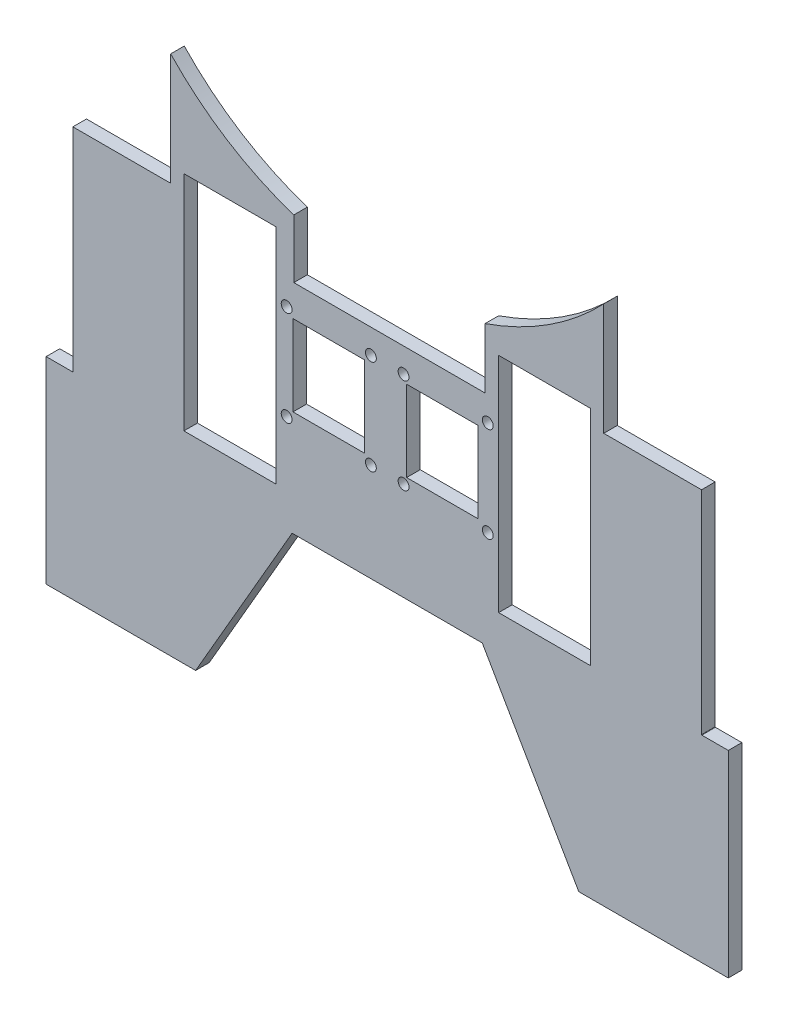
SolidWorks part; units mm, degrees
ref_plane "Front Plane" through (0, 0, 0) normal (0, 0, 1) x (1, 0, 0)
ref_plane "Top Plane" through (0, 0, 0) normal (0, 1, 0) x (1, 0, 0)
ref_plane "Right Plane" through (0, 0, 0) normal (1, 0, 0) x (0, 0, -1)
sketch "Sketch1" plane through (0, 0, 0) normal (0, 0, 1) x (1, 0, 0)
  line L157 (75.4494, -29.1887) -> (75.4494, 52.8429)
  line L158 (41.6114, -29.1887) -> (75.4494, -29.1887)
  line L159 (41.6114, 52.8429) -> (41.6114, -29.1887)
  line L160 (75.4494, 52.8429) -> (41.6114, 52.8429)
  line L161 (-74.2583, -29.1887) -> (-40.4202, -29.1887)
  line L162 (-40.4202, -29.1887) -> (-40.4202, 52.8429)
  line L163 (-74.2583, 52.8429) -> (-74.2583, -29.1887)
  line L164 (-40.4202, 52.8429) -> (-74.2583, 52.8429)
  line L165 (-67.3773, 102.2973) -> (-124.9367, 102.2973)
  line L166 (-124.9367, 102.2973) -> (-124.9535, 82.5555)
  line L169 (-124.9535, 82.5555) -> (-124.9586, 69.1219)
  line L170 (-124.9586, 69.1219) -> (-124.9589, 54.5006)
  line L171 (-124.9589, 54.5006) -> (-115.1164, 54.5006)
  line L172 (-115.1164, 54.5006) -> (-115.1164, -30.8464)
  line L173 (-115.1164, -30.8464) -> (-124.9602, -30.8464)
  line L174 (-124.9602, -30.8464) -> (-124.9602, -103.4029)
  line L175 (-124.9602, -103.4029) -> (-69.9272, -103.4029)
  line L176 (-69.9272, -103.4029) -> (-34.4065, -41.8792)
  line L177 (-34.4065, -41.8792) -> (35.5976, -41.8792)
  line L178 (35.5976, -41.8792) -> (71.1183, -103.4029)
  line L179 (71.1183, -103.4029) -> (126.1513, -103.4029)
  line L180 (126.1513, -103.4029) -> (126.1513, -30.8464)
  line L181 (126.1513, -30.8464) -> (116.4345, -30.8464)
  line L182 (116.3075, -30.7195) -> (116.3075, 54.3736)
  line L183 (116.4345, 54.5006) -> (126.15, 54.5006)
  line L184 (126.15, 54.5006) -> (126.1497, 69.1118)
  line L185 (126.1497, 69.1118) -> (126.1446, 82.5656)
  line L186 (126.1446, 82.5656) -> (126.1279, 102.2973)
  line L187 (126.1279, 102.2973) -> (68.5684, 102.2973)
  arc A29 (-67.3773, 102.2973) -> (68.5684, 102.2973) centre (0.5956, 164.3939) ccw
  arc A30 (116.3075, -30.7195) -> (116.4345, -30.8464) centre (116.4345, -30.7195) ccw
  arc A31 (116.4345, 54.5006) -> (116.3075, 54.3736) centre (116.4345, 54.3736) ccw
  circle A32 centre (-5.4202, -5.6729) radius 2
  circle A33 centre (-36.4202, -5.6729) radius 2
  circle A34 centre (-36.4202, 29.3271) radius 2
  circle A35 centre (-5.4202, 29.3271) radius 2
  circle A36 centre (6.6114, 29.3271) radius 2
  circle A37 centre (6.6114, -5.6729) radius 2
  circle A38 centre (37.6114, -5.6729) radius 2
  circle A39 centre (37.6114, 29.3271) radius 2
extrude "Boss-Extrude1" add sketch "Sketch1" along normal blind 5
sketch "Sketch6" plane through (0, 0, 5) normal (0, 0, 1) x (1, 0, 0)
  line L0 (-36.4202, 29.3271) -> (-5.4202, -5.6729) construction
  line L1 (0, 0) -> (0, 20.5502) construction
  line L2 (-34.0996, 26.707) -> (-7.7409, 26.707)
  line L3 (-34.0996, 26.707) -> (-34.0996, -3.0529)
  line L4 (-34.0996, -3.0529) -> (-7.7409, -3.0529)
  line L5 (-7.7409, 26.707) -> (-7.7409, -3.0529)
  line L6 (-34.0996, 26.707) -> (-7.7409, -3.0529) construction
  line L7 (-34.0996, -3.0529) -> (-7.7409, 26.707) construction
  line L8 (34.0996, -3.0529) -> (7.7409, 26.707) construction
  line L9 (34.0996, 26.707) -> (7.7409, -3.0529) construction
  line L10 (7.7409, 26.707) -> (7.7409, -3.0529)
  line L11 (34.0996, -3.0529) -> (7.7409, -3.0529)
  line L12 (34.0996, 26.707) -> (34.0996, -3.0529)
  line L13 (34.0996, 26.707) -> (7.7409, 26.707)
  point P4 (-20.9202, 11.8271)
  point P16 (20.9202, 11.8271)
  dimension "D1" = 3.5
extrude "Cut-Extrude5" cut sketch "Sketch6" against normal blind 10
sketch "Sketch7" plane through (0, 0, 5) normal (0, 0, 1) x (1, 0, 0)
  line L0 (30.5956, 58.3271) -> (-29.4044, 58.3271) construction
  line L1 (30.5956, 72.3271) -> (30.5956, 44.3271) construction
  line L2 (-29.4044, 44.3271) -> (-29.4044, 72.3271) construction
  line L3 (41.6114, 34.3271) -> (2.6114, 34.3271) construction
  line L5 (36.6114, 79.276) -> (36.6114, 38.3271)
  line L6 (36.6114, 38.3271) -> (-33.7889, 38.3271)
  line L7 (-33.7889, 77.4212) -> (-33.7889, 38.3271)
  line L8 (36.6114, 79.276) -> (-33.7889, 38.3271) construction
  line L9 (36.6114, 38.3271) -> (-33.7889, 77.4212) construction
  line L10 (41.6114, 52.8429) -> (41.6114, -29.1887) construction
  line L13 (36.6114, 79.276) -> (36.6114, 95.1212)
  line L14 (36.6114, 95.1212) -> (-33.7889, 95.1212)
  line L15 (-33.7889, 77.4212) -> (-33.7889, 95.1212)
  line L16 (36.6114, 79.276) -> (-33.7889, 95.1212) construction
  line L17 (36.6114, 95.1212) -> (-33.7889, 77.4212) construction
  point P7 (0.5956, 58.3271)
  point P19 (3.3575, 86.7605)
  dimension "D1" = 4
  dimension "D2" = 5
extrude "Cut-Extrude7" cut sketch "Sketch7" against normal blind 10
sketch "Sketch8" plane through (0, 0, 0) normal (0, 0, -1) x (-1, 0, 0)
  circle A0 centre (-0.5956, 164.3939) radius 110
  dimension "D1" = 220
extrude "Cut-Extrude8" cut sketch "Sketch8" against normal blind 10
sketch "Sketch9" plane through (0, 0, 5) normal (0, 0, 1) x (1, 0, 0)
  line L1 (-124.9367, 110.3271) -> (-90.201, 110.3271)
  line L2 (-124.9367, 110.3271) -> (-124.9367, 102.2973)
  line L3 (-124.9367, 102.2973) -> (-90.201, 102.2973)
  line L4 (-90.201, 110.3271) -> (-90.201, 102.2973)
  line L5 (-124.9367, 110.3271) -> (-90.201, 102.2973) construction
  line L6 (-124.9367, 102.2973) -> (-90.201, 110.3271) construction
  line L7 (126.1279, 110.3271) -> (91.3922, 110.3271)
  line L8 (126.1279, 110.3271) -> (126.1279, 102.2973)
  line L9 (126.1279, 102.2973) -> (91.3922, 102.2973)
  line L10 (91.3922, 110.3271) -> (91.3922, 102.2973)
  line L11 (126.1279, 110.3271) -> (91.3922, 102.2973) construction
  line L12 (126.1279, 102.2973) -> (91.3922, 110.3271) construction
  point P4 (-107.5689, 106.3122)
  point P11 (108.76, 106.3122)
extrude "Boss-Extrude2" add sketch "Sketch9" against normal blind 5
sketch "Sketch10" plane through (0, 0, 5) normal (0, 0, 1) x (1, 0, 0)
  line L0 (111.3075, 50.3271) -> (83.3075, 50.3271) construction
  line L1 (80.3075, 116.852) -> (127.5628, 116.852)
  line L2 (80.3075, 116.852) -> (80.3075, 47.3271)
  line L3 (80.3075, 47.3271) -> (127.5628, 47.3271)
  line L4 (127.5628, 116.852) -> (127.5628, 47.3271)
  line L5 (80.3075, 116.852) -> (127.5628, 47.3271) construction
  line L6 (80.3075, 47.3271) -> (127.5628, 116.852) construction
  line L7 (0.5956, -41.8792) -> (0.5956, -53.7447) construction
  line L8 (-34.4065, -41.8792) -> (35.5976, -41.8792) construction
  line L9 (-79.1164, 47.3271) -> (-126.3716, 116.852) construction
  line L10 (-79.1164, 116.852) -> (-126.3716, 47.3271) construction
  line L11 (-126.3716, 116.852) -> (-126.3716, 47.3271)
  line L12 (-79.1164, 47.3271) -> (-126.3716, 47.3271)
  line L13 (-79.1164, 116.852) -> (-79.1164, 47.3271)
  line L14 (-79.1164, 116.852) -> (-126.3716, 116.852)
  line L15 (83.3075, 50.3271) -> (83.3075, 110.3271) construction
  point P4 (103.9351, 82.0895)
  point P16 (-102.744, 82.0895)
  point P17 (0, 0)
  point P18 (0, 0)
  dimension "D1" = 3
  dimension "D2" = 3
extrude "Cut-Extrude9" cut sketch "Sketch10" against normal blind 10
